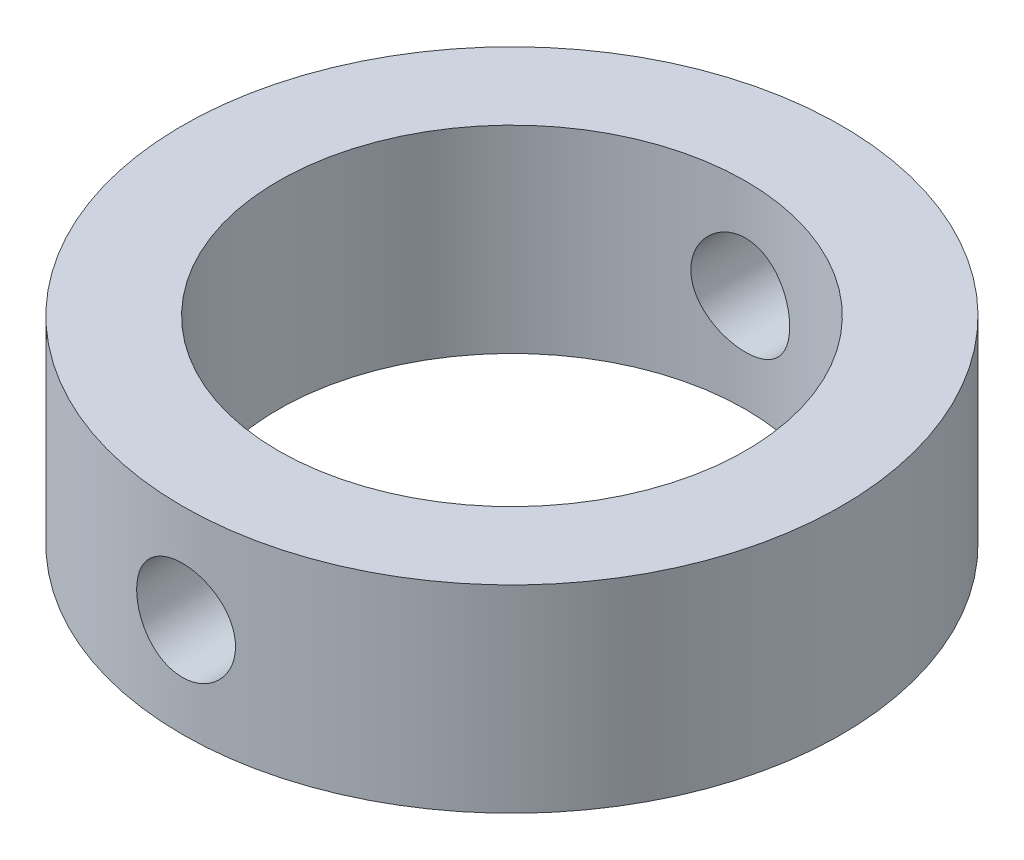
SolidWorks part; units mm, degrees
ref_plane "Front Plane" through (0, 0, 0) normal (0, 0, 1) x (1, 0, 0)
ref_plane "Top Plane" through (0, 0, 0) normal (0, 1, 0) x (1, 0, 0)
ref_plane "Right Plane" through (0, 0, 0) normal (1, 0, 0) x (0, 0, -1)
sketch "Sketch1" plane through (0, 0, 0) normal (0, 1, 0) x (1, 0, 0)
  circle A0 centre (0, 0) radius 25
  circle A1 centre (0, 0) radius 17.7222
  dimension "D1" = 35.4444
  dimension "D2" = 50
extrude "Boss-Extrude1" add sketch "Sketch1" along normal mid plane 15
sketch "Sketch2" plane through (0, 0, 0) normal (0, 0, 1) x (1, 0, 0)
  circle A0 centre (0, 0) radius 3.75
  dimension "D1" = 7.5
extrude "Cut-Extrude1" cut sketch "Sketch2" against normal through all both and the other way through all
